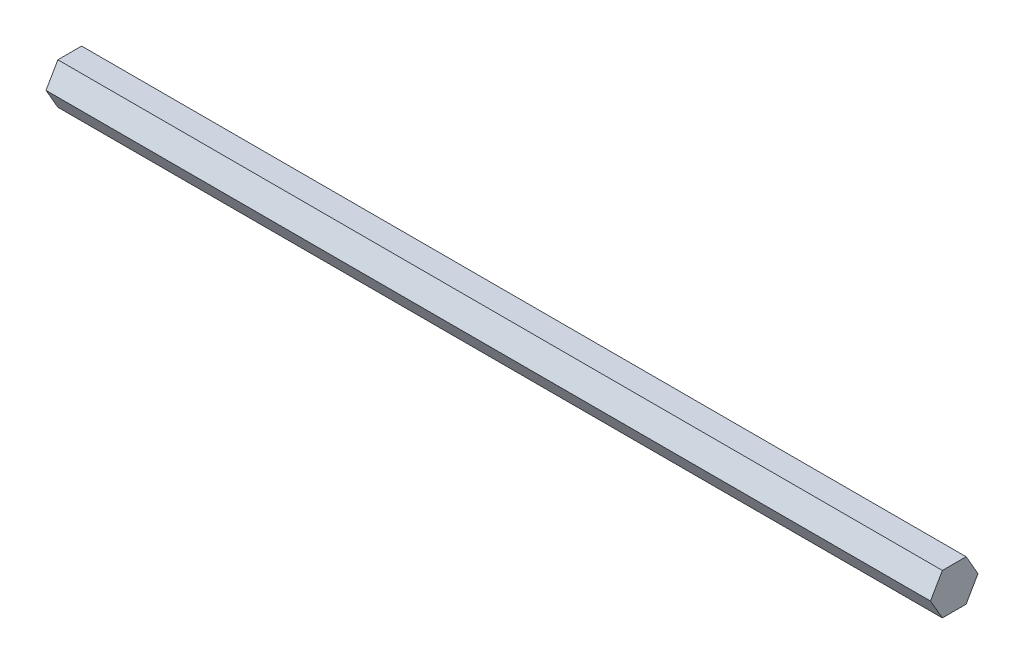
SolidWorks part; units mm, degrees
ref_plane "Front Plane" through (0, 0, 0) normal (0, 0, 1) x (1, 0, 0)
ref_plane "Top Plane" through (0, 0, 0) normal (0, 1, 0) x (1, 0, 0)
ref_plane "Right Plane" through (0, 0, 0) normal (1, 0, 0) x (0, 0, -1)
sketch "Sketch1" plane through (0, 0, 0) normal (1, 0, 0) x (0, 0, -1)
  line L1 (7.3323, 0) -> (3.6662, 6.35)
  line L2 (3.6662, 6.35) -> (-3.6662, 6.35)
  line L3 (-3.6662, 6.35) -> (-7.3323, 0)
  line L4 (-7.3323, 0) -> (-3.6662, -6.35)
  line L5 (-3.6662, -6.35) -> (3.6662, -6.35)
  line L6 (3.6662, -6.35) -> (7.3323, 0)
  circle A0 centre (0, 0) radius 6.35 construction
  dimension "D1" = 12.7
extrude "Boss-Extrude1" add sketch "Sketch1" along normal blind 273.05
